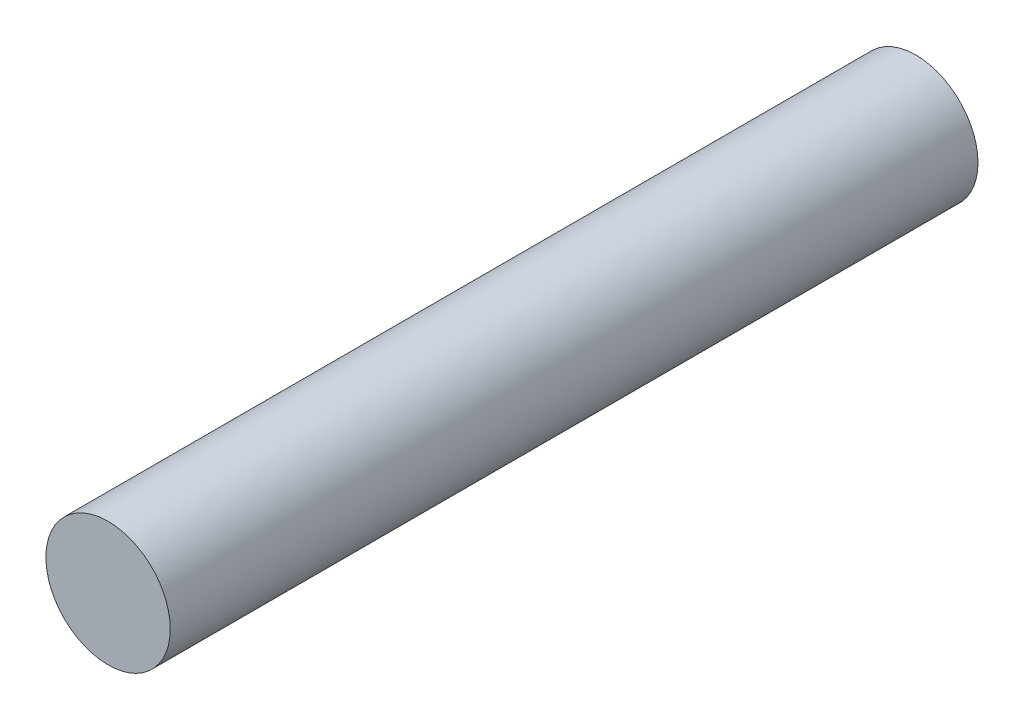
SolidWorks part; units mm, degrees
ref_plane "Front Plane" through (0, 0, 0) normal (0, 0, 1) x (1, 0, 0)
ref_plane "Top Plane" through (0, 0, 0) normal (0, 1, 0) x (1, 0, 0)
ref_plane "Right Plane" through (0, 0, 0) normal (1, 0, 0) x (0, 0, -1)
sketch "Sketch2" plane through (0, 0, 0) normal (0, 0, 1) x (1, 0, 0)
  circle A0 centre (0, 0) radius 1.1303
extrude "Extrude1" add sketch "Sketch2" along normal blind 14.6812
